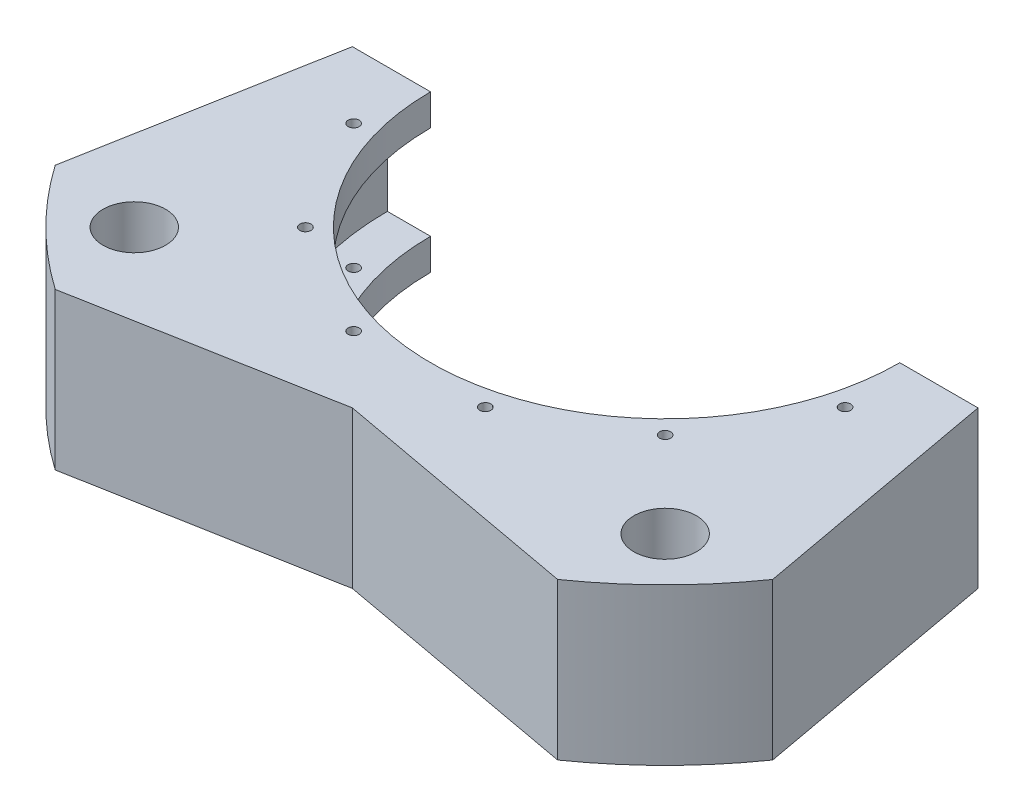
SolidWorks part; units mm, degrees
material "6061-T6 (SS)"
ref_plane "Front Plane" through (0, 0, 0) normal (0, 0, 1) x (1, 0, 0)
ref_plane "Top Plane" through (0, 0, 0) normal (0, 1, 0) x (1, 0, 0)
ref_plane "Right Plane" through (0, 0, 0) normal (1, 0, 0) x (0, 0, -1)
sketch "Sketch1" plane through (0, 0, 0) normal (0, 0, 1) x (1, 0, 0)
  line L0 (0, 0) -> (56.388, 0) construction
  line L1 (56.388, 0) -> (56.388, 9.525)
  line L2 (56.388, 0) -> (56.388, -9.525)
  line L3 (56.388, 9.525) -> (47.625, 9.525)
  line L4 (56.388, -9.525) -> (47.625, -9.525)
  line L5 (47.625, 9.525) -> (47.625, 15.875)
  line L6 (47.625, 15.875) -> (88.9, 15.875)
  line L7 (47.625, -9.525) -> (47.625, -15.875)
  line L8 (47.625, -15.875) -> (88.9, -15.875)
  line L9 (88.9, 15.875) -> (88.9, -15.875)
  line L10 (0, 22.5393) -> (0, -21.157) construction
  dimension "D1" = 56.388
  dimension "D2" = 9.525
  dimension "D3" = 9.525
  dimension "D4" = 47.625
  dimension "D5" = 6.35
  dimension "D6" = 6.35
  dimension "D7" = 88.9
  dimension "D8" = 47.625
revolve "Revolve1" add sketch "Sketch1" angle 180 about L10
sketch "Sketch2" plane through (0, 15.875, 0) normal (0, 1, 0) x (1, 0, 0)
  line L0 (49.8787, -13.3649) -> (0, 0) construction
  line L1 (0, 0) -> (55.1424, 0) construction
  line L2 (88.9, 0) -> (47.625, 0) construction
  point P4 (49.8787, -13.3649)
  dimension "D1" = 15
  dimension "D2" = 51.6382
hole_wizard "Tap Drill for #4-40 Tap1" positions "3DSketch1" profile "Sketch3" hole size "#4-40" standard "ANSI Inch" end condition through all
sketch3d "3DSketch1"
  point P0 (49.8787, 15.875, 13.3649)
sketch "Sketch3" plane through (49.8787, 15.875, 13.3649) normal (1, 0, 0) x (0, 0, 1)
  line L0 (0, 0) -> (0, 31.75)
  line L1 (0, 31.75) -> (1.1303, 31.75)
  line L2 (1.1303, 31.75) -> (1.1303, 0)
  line L5 (1.1303, 0) -> (0, 0)
  line L11 (0, -6.35) -> (0, 107.95) construction
  dimension "Thru Hole Dia." = 2.2606
  dimension "Thru Hole Depth" = 31.75
pattern_circular "CirPattern1" count 12 over 360 about axis through (0, 15.875, 0) along (0, 1, 0) skipping 1, 2, 3, 4, 5, 6 of "Tap Drill for #4-40 Tap1"
sketch "Sketch4" plane through (0, 0, 0) normal (0, 0, -1) x (-1, 0, 0)
  line L2 (47.625, -15.875) -> (88.9, -15.875) construction
  line L3 (88.9, -15.875) -> (88.9, 15.875) construction
  circle A0 centre (82.55, 6.35) radius 1.1303
  circle A1 centre (82.55, -6.35) radius 1.1303
  dimension "D1" = 2.2606
  dimension "D2" = 2.2606
  dimension "D3" = 12.7
  dimension "D4" = 6.35
  dimension "D5" = 9.525
  dimension "D6" = 6.35
extrude "Cut-Extrude1" cut sketch "Sketch4" against normal up to next
sketch "Sketch6" plane through (0, 0, 0) normal (0, 0, -1) x (-1, 0, 0)
  line L0 (-88.9, -15.875) -> (-88.9, 15.875) construction
  line L1 (-47.625, -15.875) -> (-88.9, -15.875) construction
  circle A0 centre (-82.55, 6.35) radius 1.1303
  circle A1 centre (-82.5792, -6.35) radius 1.1303
  dimension "D3" = 2.2606
  dimension "D4" = 2.2606
  dimension "D1" = 6.35
  dimension "D2" = 9.525
  dimension "D5" = 12.7
extrude "Cut-Extrude2" cut sketch "Sketch6" against normal up to next and the other way through all
sketch "Sketch7" plane through (0, 15.875, 0) normal (0, 1, 0) x (1, 0, 0)
  line L0 (88.9, 0) -> (47.625, 0) construction
  line L1 (-88.9, 0) -> (-47.625, 0) construction
  line L2 (0, 0) -> (0, -88.9) construction
  line L3 (0, 0) -> (-70.8597, -101.1982) construction
  line L4 (0, 0) -> (74.4736, -106.3593) construction
  line L5 (50.9909, -72.8226) -> (0, -63.5)
  line L6 (0, 0) -> (111.1038, 0) construction
  line L7 (53.8815, -53.8815) -> (0, 0) construction
  line L8 (0, 0) -> (-96.8039, 0) construction
  line L9 (0, 0) -> (-77.4, -77.4) construction
  line L10 (0, -63.5) -> (-50.9909, -72.8226)
  line L11 (72.8226, -50.9909) -> (63.5, 0)
  line L12 (0, 0) -> (127.391, -89.2001) construction
  line L13 (0, 0) -> (-97.05, -67.9551) construction
  line L14 (-72.8226, -50.9909) -> (-63.5, 0)
  arc A0 (63.5, 0) -> (-63.5, 0) centre (0, 0) cw
  circle A3 centre (53.8815, -53.8815) radius 6.35
  circle A4 centre (-53.8815, -53.8815) radius 6.35
  arc A5 (-88.9, 0) -> (88.9, 0) centre (0, 0) ccw construction
  arc A6 (50.9909, -72.8226) -> (-50.9909, -72.8226) centre (0, 0) cw
  arc M12 (-88.9, 0) -> (88.9, 0) centre (0, 0) ccw
  line M13 (88.9, 0) -> (47.625, 0)
  line M15 (-47.625, 0) -> (-88.9, 0)
  dimension "D1" = 63.5
  dimension "D2" = 12.7
  dimension "D6" = 12.7
  dimension "D3" = 76.2
  dimension "D4" = 45
  dimension "D5" = 45
  dimension "D7" = 76.2
  dimension "D8" = 35
  dimension "D9" = 35
  dimension "D10" = 35
  dimension "D11" = 35
extrude "Cut-Extrude3" cut sketch "Sketch7" against normal up to next contours A3 | A4 | L5 L10 M12 | L11 M12 M13 | L14 M12 M15
